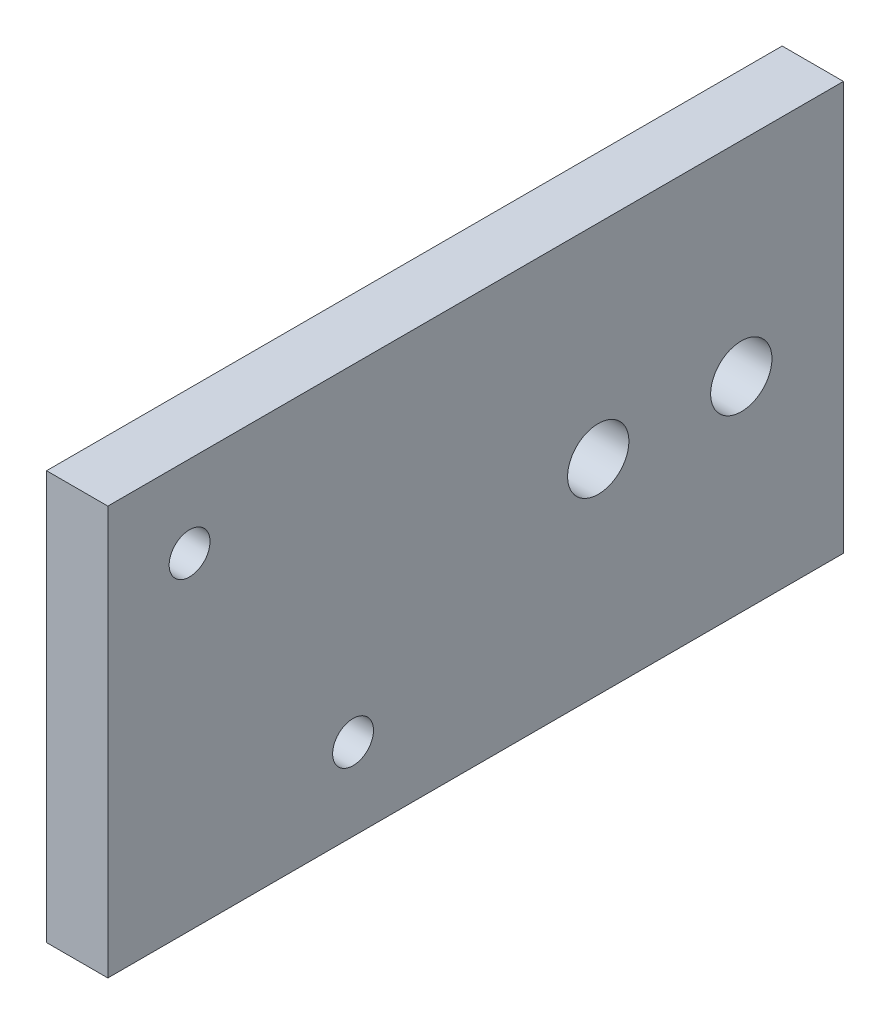
SolidWorks part; units mm, degrees
ref_plane "Front Plane" through (0, 0, 0) normal (0, 0, 1) x (1, 0, 0)
ref_plane "Top Plane" through (0, 0, 0) normal (0, 1, 0) x (1, 0, 0)
ref_plane "Right Plane" through (0, 0, 0) normal (1, 0, 0) x (0, 0, -1)
sketch "Croquis1" plane through (0, 0, 0) normal (1, 0, 0) x (0, 0, -1)
  line L0 (-18, -10) -> (-18, 10)
  line L1 (-18, -10) -> (18, -10)
  line L2 (-18, 10) -> (18, 10)
  line L3 (18, -10) -> (18, 10)
  line L4 (-18, -10) -> (18, 10) construction
  line L5 (-18, 10) -> (18, -10) construction
  line L6 (0, 0) -> (0, 10)
  line L7 (0, 0) -> (0, -10)
  line L8 (-3, 10) -> (-3, -10)
  line L9 (-18, 10) -> (-21, 10)
  line L10 (-21, 10) -> (-21, -10)
  line L11 (-21, -10) -> (-18, -10)
  circle A0 centre (13, 0) radius 1.5
  circle A1 centre (6, 0) radius 1.5
  point P1 (0, 0)
  dimension "D4" = 6
  dimension "D5" = 3
  dimension "D6" = 3
  dimension "D1" = 18
  dimension "D2" = 20
  dimension "D3" = 5
  dimension "D7" = 10
  dimension "D8" = 10
  dimension "D9" = 3
  dimension "D10" = 3
extrude "Saliente-Extruir1" add sketch "Croquis1" along normal blind 3 contours L8 L2 L0 L1 | L6 L7 L1 L3 L2 A1 A0 | L2 L8 L1 L7 L6
sketch "Croquis2" plane through (3, 0, 0) normal (1, 0, 0) x (0, 0, -1)
  line L0 (-18, 10) -> (18, 10) construction
  line L1 (-18, -10) -> (-18, 10) construction
  line L2 (-18, -10) -> (18, -10) construction
  circle A0 centre (-14, 6) radius 1
  circle A1 centre (-6, -6) radius 1
  dimension "D5" = 2
  dimension "D6" = 2
  dimension "D1" = 4
  dimension "D2" = 4
  dimension "D3" = 4
  dimension "D4" = 6
extrude "Cortar-Extruir1" cut sketch "Croquis2" against normal blind 10
